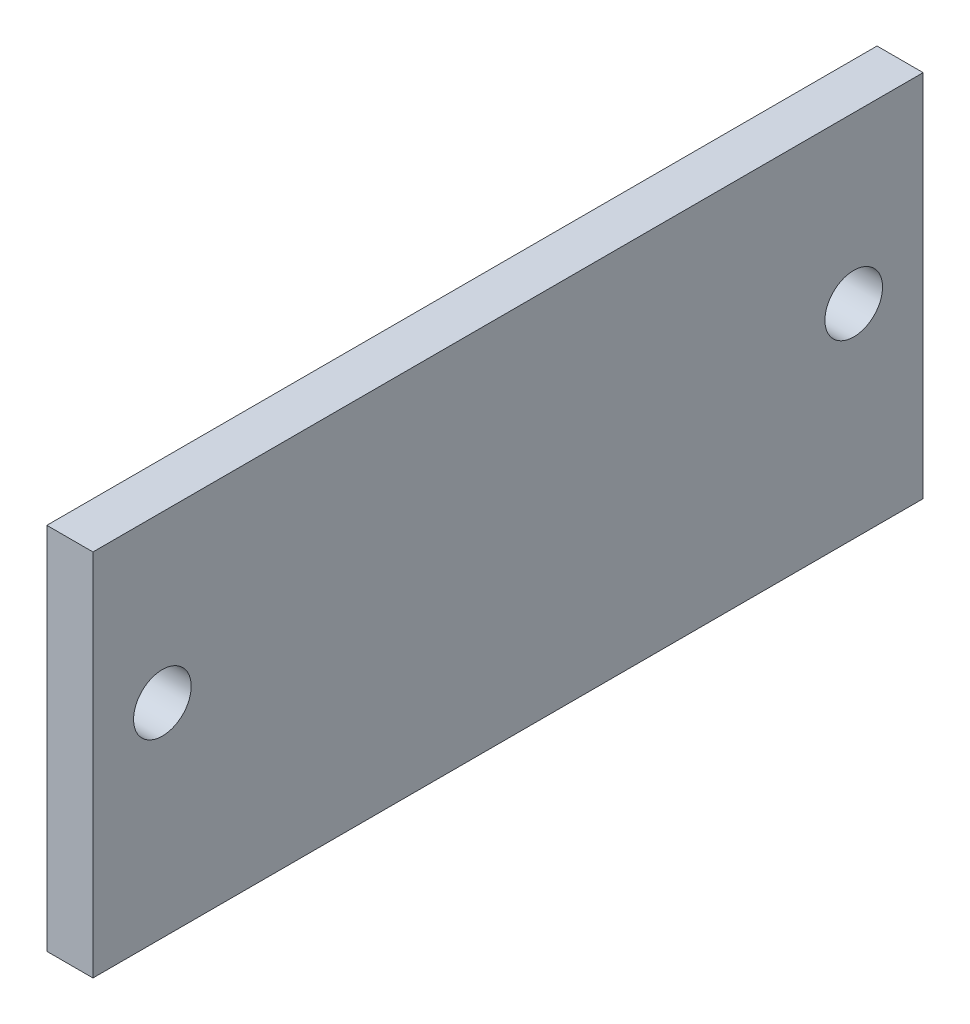
SolidWorks part; units mm, degrees
material "Ceramic Porcelain"
ref_plane "Front Plane" through (0, 0, 0) normal (0, 0, 1) x (1, 0, 0)
ref_plane "Top Plane" through (0, 0, 0) normal (0, 1, 0) x (1, 0, 0)
ref_plane "Right Plane" through (0, 0, 0) normal (1, 0, 0) x (0, 0, -1)
sketch "Sketch1" plane through (0, 0, 0) normal (1, 0, 0) x (0, 0, -1)
  line L1 (114.3, 50.8) -> (-114.3, 50.8)
  line L2 (114.3, 50.8) -> (114.3, -50.8)
  line L3 (114.3, -50.8) -> (-114.3, -50.8)
  line L4 (-114.3, 50.8) -> (-114.3, -50.8)
  line L5 (0, -50.8) -> (0, 50.8) construction
  line L6 (114.3, 0) -> (-114.3, 0) construction
  point P0 (0, 0)
  dimension "D1" = 228.6
  dimension "D2" = 101.6
extrude "Boss-Extrude1" add sketch "Sketch1" against normal blind 12.7
sketch "Sketch2" plane through (0, 0, 0) normal (1, 0, 0) x (0, 0, -1)
  line L0 (101.092, -0.889) -> (89.281, -0.889) construction
  line L1 (89.281, -0.889) -> (89.281, 11.43) construction
  line L2 (89.281, 11.43) -> (101.092, 11.43) construction
  line L3 (-89.281, 11.43) -> (-89.281, -0.889) construction
  line L4 (-89.281, -0.889) -> (-101.092, -0.889) construction
  line L5 (-101.092, 11.43) -> (-89.281, 11.43) construction
  line L6 (101.092, -0.889) -> (89.281, -0.889)
  line L7 (89.281, -0.889) -> (89.281, 11.43)
  line L8 (89.281, 11.43) -> (101.092, 11.43)
  line L9 (-89.281, 11.43) -> (-89.281, -0.889)
  line L10 (-89.281, -0.889) -> (-101.092, -0.889)
  line L11 (-101.092, 11.43) -> (-89.281, 11.43)
  line L12 (-95.1865, 11.43) -> (-95.1865, -0.889) construction
  circle A0 centre (-95.1865, 5.2705) radius 7.9375
  dimension "D1" = 15.875
extrude "Cut-Extrude1" cut sketch "Sketch2" against normal up to next (12.7 mm away) contours A0
mirror "Mirror1" about plane through (0, 0, 0) normal (0, 0, 1) of "Cut-Extrude1"
